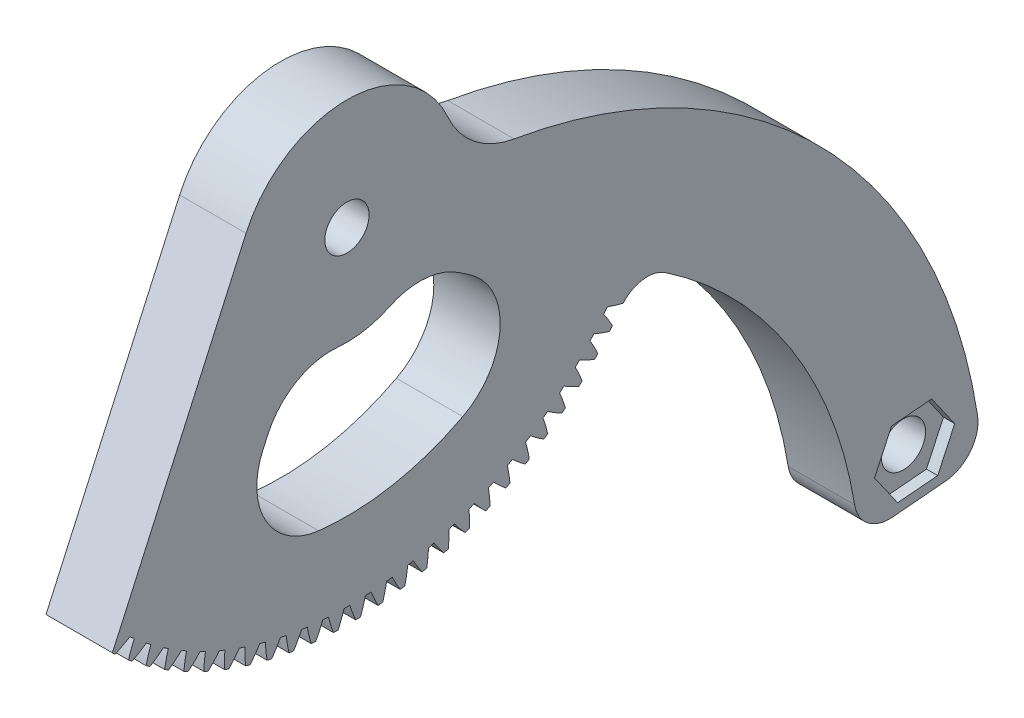
SolidWorks part; units mm, degrees
ref_plane "Plane1" through (0, 0, 0) normal (0, 0, 1) x (1, 0, 0)
ref_plane "Plane2" through (0, 0, 0) normal (0, 1, 0) x (1, 0, 0)
ref_plane "Plane3" through (0, 0, 0) normal (1, 0, 0) x (0, 0, -1)
sketch "HoldingSke" plane through (0, 0, 0) normal (0, 1, 0) x (1, 0, 0)
  line L0 (0, 0) -> (-0.1045, -0.9945)
  line L1 (-15, 0) -> (100, 0) construction
  line L2 (0, 0) -> (-2.1039, 2.3779)
  line L3 (0, 0) -> (-11.863, 4.5341)
  line L4 (0, 0) -> (-0.9027, 8.5887)
  line L5 (0, 0) -> (-46.8476, -17.4728)
  line L6 (0, 0) -> (-10.5278, -7.1032)
  line L7 (-2.1039, 2.3779) -> (8.6586, 51.2059)
  line L8 (-76.2, 54.61) -> (-76.1, 54.61)
  line L9 (-71.009, 38.7566) -> (-53.1078, 45.2721)
  line L10 (-76.2, 71.12) -> (104.1128, 71.12)
  line L11 (0, 0) -> (-12.7, 0)
  line L12 (-76.2, 101.6) -> (-76.162, 101.6)
  line L13 (24.9733, 27.94) -> (52.9518, 28.4284)
  line L14 (24.9733, 27.94) -> (24.9743, 27.94)
  line L15 (24.9733, 27.94) -> (100.4006, 29.5858)
  line L16 (-63.627, -1) -> (-12.827, -1)
  circle A0 centre (0, 0) radius 0.4
  circle A1 centre (0, 0) radius 37.5
  circle A2 centre (0, 0) radius 37.5
  circle A3 centre (0, 0) radius 0.4
  dimension "MHD" = 75
  dimension "Hub_dia" = 75
  dimension "Bore" = 0.8
  dimension "MBD" = 0.8
  dimension "Num_teeth" = 96
  dimension "Pitch" = 1
  dimension "Overall_len" = 50
  dimension "Show_teeth" = 96
  dimension "Thickness" = 12.7
  dimension "OAL" = 50.0001
  dimension "T_dim" = 0.1
  dimension "Ap" = 20
  dimension "H" = 19.05
  dimension "Pitch_radius" = 180.3128
  dimension "Width" = 12.7
  dimension "Backlash" = 0.038
  dimension "Addendum_fac" = 1
  dimension "Dedendum_fac" = 1.25
  dimension "Clearance_fac" = 0.25
  dimension "Dedendum_add" = 0.001
  dimension "Module" = 1
sketch "BasProSke" plane through (0, 0, 0) normal (0, 1, 0) x (1, 0, 0)
  line L0 (-10, 0) -> (60, 0) construction
  line L1 (0, 0) -> (0, 49)
  line L2 (0, 0) -> (12.7, 0)
  line L3 (12.7, 0) -> (12.7, 49)
  line L4 (12.7, 49) -> (0, 49)
  dimension "Thickness" = 12.7
  dimension "Diameter" = 98
revolve "Base-Revolve" add sketch "BasProSke" angle 360 about L0
sketch "TooCutSke" plane through (0, 0, 0) normal (1, 0, 0) x (0, 0, -1)
  line L1 (0, 0) -> (0, 107) construction
  line L2 (0, 0) -> (-0.8519, 47.9924) construction
  line L3 (0, 0) -> (-3.1407, 95.9378) construction
  line L4 (-0.8519, 47.9924) -> (-1.5703, 47.9689) construction
  arc A0 (0.4157, 46.7472) -> (-0.4157, 46.7472) centre (0, 0) ccw
  arc A1 (1.2815, 49.0086) -> (-1.2815, 49.0086) centre (0, 0) ccw
  circle A2 centre (0, 0) radius 48 construction
  circle A3 centre (0, 0) radius 45.1052 construction
  arc A4 (-0.4157, 46.7472) -> (-1.2815, 49.0086) centre (-18.7436, 41.0264) ccw
  arc A5 (1.2815, 49.0086) -> (0.4157, 46.7472) centre (18.7436, 41.0264) ccw
  dimension "Root_dia" = 93.498
  dimension "Overcut_dia" = 98.0508
  dimension "Pitch_dia" = 96
  dimension "Base_dia" = 90.2105
  dimension "Flank_rad" = 19.2
  dimension "Half_ang" = 1.875
  dimension "Half_CT" = 0.7189
extrude "ToothCut" cut sketch "TooCutSke" along normal through all
fillet "Breaks" [suppressed] radius 0.02
fillet "RootFillets" [suppressed] radius 0.251
pattern_circular "TeethCuts" count 96 over 360 about axis through (0, 0, 0) along (1, 0, 0) of "ToothCut", "RootFillets", "Breaks"
sketch "HubNeaOneSke" plane through (0, 0, 0) normal (-1, 0, 0) x (0, 0, 1)
  circle A0 centre (0, 0) radius 37.5
  dimension "Diameter" = 75
extrude "HubNearOne" [suppressed] add sketch "HubNeaOneSke" along normal blind 37.3001
sketch "HubNeaBotSke" plane through (0, 0, 0) normal (-1, 0, 0) x (0, 0, 1)
  circle A0 centre (0, 0) radius 37.5
  dimension "Diameter" = 75
extrude "HubNearBoth" [suppressed] add sketch "HubNeaBotSke" along normal blind 18.65
ref_plane "FarPln" through (12.7, 0, 0) normal (1, 0, 0) x (0, 0, -1)
sketch "HubFarSke" plane through (12.7, 0, 0) normal (1, 0, 0) x (0, 0, -1)
  circle A0 centre (0, 0) radius 37.5
  dimension "Diameter" = 75
extrude "HubFar" [suppressed] add sketch "HubFarSke" along normal blind 18.65
sketch "BorSke" plane through (0, 0, 0) normal (1, 0, 0) x (0, 0, -1)
  circle A0 centre (0, 0) radius 0.4
  dimension "Diameter" = 0.8
extrude "Bore" cut sketch "BorSke" along normal mid plane 100.0001
sketch "KeySke" plane through (0, 0, 0) normal (1, 0, 0) x (0, 0, -1)
  line L0 (-0.05, 0) -> (-0.05, 0.5)
  line L1 (-0.05, 0.5) -> (0.05, 0.5)
  line L2 (0.05, 0.5) -> (0.05, 0)
  line L3 (0, 0) -> (0, 34) construction
  line L4 (-0.05, 0) -> (0.05, 0)
  dimension "Offset" = 0.5
  dimension "Width" = 0.1
extrude "Keyway" [suppressed] cut sketch "KeySke" along normal mid plane 100.0001
pattern_circular "Keyway2" [suppressed] count 2 every 90 about axis through (-10, 0, 0) along (1, 0, 0)
sketch "Croquis2" plane through (12.7, 0, 0) normal (1, 0, 0) x (0, 0, -1)
  line L4 (78.2913, -74.7181) -> (85.9012, -74.0523)
  line L5 (-14.4729, 6.923) -> (-33.6475, -35.6208)
  arc A0 (-33.6475, -35.6208) -> (40.4538, -27.7628) centre (0, 0.4) ccw
  arc A1 (48.3959, -8.954) -> (40.4538, -27.7628) centre (0, 0.4) ccw
  arc A2 (-33.7385, -35.5347) -> (-33.252, -35.9904) centre (0, 0) ccw construction
  arc A66 (85.9012, -74.0523) -> (90.4783, -68.2125) centre (85.4584, -68.9917) ccw
  arc A67 (90.4783, -68.2125) -> (23.9847, -0.5832) centre (10.16, -80.6788) ccw
  arc A68 (14.5249, 6.8066) -> (23.9847, -0.5832) centre (26.1448, 11.9318) ccw
  arc A69 (14.5249, 6.8066) -> (-14.4729, 6.923) centre (0, 0.4) ccw
  arc A96 (45.6754, -28.0395) -> (40.4538, -27.7628) centre (42.8342, -32.2506) ccw
  arc A97 (72.8346, -70.4738) -> (45.6754, -28.0395) centre (10.16, -80.6788) ccw
  arc A98 (72.8346, -70.4738) -> (78.2913, -74.7181) centre (77.8486, -69.6574) ccw
extrude "Cortar-Extruir1" cut sketch "Croquis2" against normal through all contours A69 A68 A67 A1 L5
sketch "Croquis3" plane through (12.7, 0, 0) normal (1, 0, 0) x (0, 0, -1)
  line L0 (78.2913, -74.7181) -> (85.9012, -74.0523) construction
  line L1 (78.2913, -74.7181) -> (85.9012, -74.0523)
  line L2 (23.9847, -0.5832) -> (26.1016, -24.7798)
  line L4 (39.6344, -28.8117) -> (26.1016, -24.7798)
  arc A1 (90.4783, -68.2125) -> (23.9847, -0.5832) centre (10.16, -80.6788) ccw construction
  arc A2 (85.9012, -74.0523) -> (90.4783, -68.2125) centre (85.4584, -68.9917) ccw construction
  arc A3 (72.8346, -70.4738) -> (78.2913, -74.7181) centre (77.8486, -69.6574) ccw construction
  arc A4 (72.8346, -70.4738) -> (45.6754, -28.0395) centre (10.16, -80.6788) ccw construction
  arc A6 (90.4783, -68.2125) -> (23.9847, -0.5832) centre (10.16, -80.6788) ccw
  arc A7 (85.9012, -74.0523) -> (90.4783, -68.2125) centre (85.4584, -68.9917) ccw
  arc A8 (72.8346, -70.4738) -> (78.2913, -74.7181) centre (77.8486, -69.6574) ccw
  arc A9 (72.8346, -70.4738) -> (45.6754, -28.0395) centre (10.16, -80.6788) ccw
  arc A13 (39.6344, -28.8117) -> (45.6754, -28.0395) centre (43.0946, -31.8647) cw
extrude "Saliente-Extruir1" add sketch "Croquis3" against normal through all
sketch "Croquis4" plane through (12.7, 0, 0) normal (1, 0, 0) x (0, 0, -1)
  line L0 (78.2913, -74.7181) -> (85.9012, -74.0523) construction
  circle A0 centre (0, 0.4) radius 3.175
  circle A1 centre (81.4431, -68.0681) radius 3.175
  arc A2 (90.4783, -68.2125) -> (23.9847, -0.5832) centre (10.16, -80.6788) ccw construction
  arc A3 (90.4783, -68.2125) -> (23.9847, -0.5832) centre (10.16, -80.6788) ccw construction
  circle A4 centre (10.16, -80.6788) radius 72.39 construction
  circle A5 centre (10.16, -80.6788) radius 81.715 construction
  arc A6 (14.5249, 6.8066) -> (-14.4729, 6.923) centre (0, 0.4) ccw construction
  point P8 (0, 0)
  dimension "D1" = 6.35
  dimension "D2" = 6.35
  dimension "D3" = 144.78
  dimension "D4" = 163.43
extrude "Cortar-Extruir2" cut sketch "Croquis4" against normal through all
sketch "Croquis5" plane through (12.7, 0, 0) normal (1, 0, 0) x (0, 0, -1)
  line L0 (78.2913, -74.7181) -> (85.9012, -74.0523) construction
  line L1 (83.8831, -62.8355) -> (78.1316, -63.3387)
  line L2 (78.1316, -63.3387) -> (75.6916, -68.5713)
  line L3 (75.6916, -68.5713) -> (79.0031, -73.3007)
  line L4 (79.0031, -73.3007) -> (84.7547, -72.7975)
  line L5 (84.7547, -72.7975) -> (87.1946, -67.5649)
  line L6 (87.1946, -67.5649) -> (83.8831, -62.8355)
  circle A0 centre (81.4431, -68.0681) radius 5 construction
  dimension "D1" = 10
extrude "Cortar-Extruir3" cut sketch "Croquis5" against normal blind 3.2 contours L1 L2 L3 L4 L5 L6
ref_plane "Plano1" through (6.35, 0, 0) normal (1, 0, 0) x (0, 0, -1)
sketch "Croquis7" plane through (12.7, 0, 0) normal (1, 0, 0) x (0, 0, -1)
  line L0 (-12.0435, -21.2056) -> (-11.3475, -19.6613)
  line L1 (17.5581, -14.2325) -> (16.023, -13.2028)
  arc A0 (-1.3117, -13.8126) -> (6.1461, -12.4819) centre (0, 0.4) ccw
  arc A1 (-4.0575, -35.2504) -> (16.619, -31.3997) centre (0, 0.4) ccw
  arc A2 (17.5581, -14.2325) -> (16.619, -31.3997) centre (11.9872, -22.5371) cw
  arc A3 (-12.0435, -21.2056) -> (-4.0575, -35.2504) centre (-2.9267, -25.3145) ccw
  arc A4 (-11.3475, -19.6613) -> (-1.3117, -13.8126) centre (-2.2307, -23.7703) cw
  arc A5 (16.023, -13.2028) -> (6.1461, -12.4819) centre (10.4522, -21.5073) ccw
  dimension "D1" = 10
extrude "Cortar-Extruir4" cut sketch "Croquis7" against normal up to surface (12.7 mm away)
sketch "Croquis8" plane through (12.7, 0, 0) normal (1, 0, 0) x (0, 0, -1)
  line L2 (78.2913, -74.7181) -> (85.9012, -74.0523)
  line L3 (-14.4729, 6.923) -> (-33.6475, -35.6208)
  line L4 (78.2913, -74.7181) -> (85.9012, -74.0523)
  line L5 (-14.4729, 6.923) -> (-33.6475, -35.6208)
  arc A111 (36.834, -28.7876) -> (37.3401, -28.1281) centre (0, 0) ccw
  arc A112 (37.3401, -28.1281) -> (39.6344, -28.8117) centre (43.9588, -10.105) ccw
  arc A113 (45.6754, -28.0395) -> (39.6344, -28.8117) centre (43.0946, -31.8647) ccw
  arc A114 (72.8346, -70.4738) -> (45.6754, -28.0395) centre (10.16, -80.6788) ccw
  arc A115 (72.8346, -70.4738) -> (78.2913, -74.7181) centre (77.8486, -69.6574) ccw
  arc A116 (85.9012, -74.0523) -> (90.4783, -68.2125) centre (85.4584, -68.9917) ccw
  arc A117 (90.4783, -68.2125) -> (23.9847, -0.5832) centre (10.16, -80.6788) ccw
  arc A118 (14.5249, 6.8066) -> (23.9847, -0.5832) centre (26.1448, 11.9318) ccw
  arc A119 (14.5249, 6.8066) -> (-14.4729, 6.923) centre (0, 0.4) ccw
  arc A120 (-33.6475, -35.6208) -> (-33.252, -35.9904) centre (0, 0) ccw
  arc A121 (-33.252, -35.9904) -> (-31.1351, -34.8723) centre (-41.1427, -18.4867) ccw
  arc A122 (-31.1351, -34.8723) -> (-30.51, -35.4204) centre (0, 0) ccw
  arc A123 (-30.51, -35.4204) -> (-31.3422, -37.6652) centre (-12.9584, -43.2037) ccw
  arc A124 (-31.3422, -37.6652) -> (-30.8269, -38.0881) centre (0, 0) ccw
  arc A125 (-30.8269, -38.0881) -> (-28.7876, -36.834) centre (-39.8455, -21.138) ccw
  arc A126 (-28.7876, -36.834) -> (-28.1281, -37.3401) centre (0, 0) ccw
  arc A127 (-28.1281, -37.3401) -> (-28.8117, -39.6344) centre (-10.105, -43.9588) ccw
  arc A128 (-28.8117, -39.6344) -> (-28.2698, -40.0227) centre (0, 0) ccw
  arc A129 (-28.2698, -40.0227) -> (-26.3169, -38.6379) centre (-38.3777, -23.6988) ccw
  arc A130 (-26.3169, -38.6379) -> (-25.6257, -39.0998) centre (0, 0) ccw
  arc A131 (-25.6257, -39.0998) -> (-26.1578, -41.4339) centre (-7.2083, -44.5255) ccw
  arc A132 (-26.1578, -41.4339) -> (-25.5917, -41.7859) centre (0, 0) ccw
  arc A133 (-25.5917, -41.7859) -> (-23.7336, -40.2764) centre (-36.7456, -26.1581) ccw
  arc A134 (-23.7336, -40.2764) -> (-23.0136, -40.6921) centre (0, 0) ccw
  arc A135 (-23.0136, -40.6921) -> (-23.3918, -43.056) centre (-4.2808, -44.9017) ccw
  arc A136 (-23.3918, -43.056) -> (-22.804, -43.3703) centre (0, 0) ccw
  arc A137 (-22.804, -43.3703) -> (-21.0485, -41.7424) centre (-34.9561, -28.5053) ccw
  arc A138 (-21.0485, -41.7424) -> (-20.3029, -42.1101) centre (0, 0) ccw
  arc A139 (-20.3029, -42.1101) -> (-20.5258, -44.4937) centre (-1.3349, -45.0855) ccw
  arc A140 (-20.5258, -44.4937) -> (-19.9186, -44.7688) centre (0, 0) ccw
  arc A141 (-19.9186, -44.7688) -> (-18.2734, -43.0297) centre (-33.0169, -30.7305) ccw
  arc A142 (-18.2734, -43.0297) -> (-17.5053, -43.3478) centre (0, 0) ccw
  arc A143 (-17.5053, -43.3478) -> (-17.5718, -45.7409) centre (1.6167, -45.0763) ccw
  arc A144 (-17.5718, -45.7409) -> (-16.9479, -45.9757) centre (0, 0) ccw
  arc A145 (-16.9479, -45.9757) -> (-15.42, -44.1327) centre (-30.9363, -32.8242) ccw
  arc A146 (-15.42, -44.1327) -> (-14.6328, -44.3999) centre (0, 0) ccw
  arc A147 (-14.6328, -44.3999) -> (-14.5426, -46.7922) centre (4.5614, -44.874) ccw
  arc A148 (-14.5426, -46.7922) -> (-13.9047, -46.9857) centre (0, 0) ccw
  arc A149 (-13.9047, -46.9857) -> (-12.5006, -45.0467) centre (-28.7233, -34.7772) ccw
  arc A150 (-12.5006, -45.0467) -> (-11.6976, -45.2619) centre (0, 0) ccw
  arc A151 (-11.6976, -45.2619) -> (-11.4511, -47.6432) centre (7.4865, -44.4796) ccw
  arc A152 (-11.4511, -47.6432) -> (-10.8019, -47.7946) centre (0, 0) ccw
  arc A153 (-10.8019, -47.7946) -> (-9.5276, -45.7678) centre (-26.3873, -36.5813) ccw
  arc A154 (-9.5276, -45.7678) -> (-8.7122, -45.93) centre (0, 0) ccw
  arc A155 (-8.7122, -45.93) -> (-8.3105, -48.2901) centre (10.3796, -43.8947) ccw
  arc A156 (-8.3105, -48.2901) -> (-7.6528, -48.3987) centre (0, 0) ccw
  arc A157 (-7.6528, -48.3987) -> (-6.5138, -46.293) centre (-23.9382, -38.2288) ccw
  arc A158 (-6.5138, -46.293) -> (-5.6896, -46.4015) centre (0, 0) ccw
  arc A159 (-5.6896, -46.4015) -> (-5.1344, -48.7303) centre (13.2282, -43.1219) ccw
  arc A160 (-5.1344, -48.7303) -> (-4.471, -48.7956) centre (0, 0) ccw
  arc A161 (-4.471, -48.7956) -> (-3.4722, -46.6199) centre (-21.3867, -39.7126) ccw
  arc A162 (-3.4722, -46.6199) -> (-2.6426, -46.6742) centre (0, 0) ccw
  arc A163 (-2.6426, -46.6742) -> (-1.9363, -48.9617) centre (16.0202, -42.1644) ccw
  arc A164 (-1.9363, -48.9617) -> (-1.2701, -48.9835) centre (0, 0) ccw
  arc A165 (-1.2701, -48.9835) -> (-0.4157, -46.7472) centre (-18.7436, -41.0264) ccw
  arc A166 (-0.4157, -46.7472) -> (0.4157, -46.7472) centre (0, 0) ccw
  arc A167 (0.4157, -46.7472) -> (1.2701, -48.9835) centre (18.7436, -41.0264) ccw
  arc A168 (1.2701, -48.9835) -> (1.9363, -48.9617) centre (0, 0) ccw
  arc A169 (1.9363, -48.9617) -> (2.6426, -46.6742) centre (-16.0202, -42.1644) ccw
  arc A170 (2.6426, -46.6742) -> (3.4722, -46.6199) centre (0, 0) ccw
  arc A171 (3.4722, -46.6199) -> (4.471, -48.7956) centre (21.3867, -39.7126) ccw
  arc A172 (4.471, -48.7956) -> (5.1344, -48.7303) centre (0, 0) ccw
  arc A173 (5.1344, -48.7303) -> (5.6896, -46.4015) centre (-13.2282, -43.1219) ccw
  arc A174 (5.6896, -46.4015) -> (6.5138, -46.293) centre (0, 0) ccw
  arc A175 (6.5138, -46.293) -> (7.6528, -48.3987) centre (23.9382, -38.2288) ccw
  arc A176 (7.6528, -48.3987) -> (8.3105, -48.2901) centre (0, 0) ccw
  arc A177 (8.3105, -48.2901) -> (8.7122, -45.93) centre (-10.3796, -43.8947) ccw
  arc A178 (8.7122, -45.93) -> (9.5276, -45.7678) centre (0, 0) ccw
  arc A179 (9.5276, -45.7678) -> (10.8019, -47.7946) centre (26.3873, -36.5813) ccw
  arc A180 (10.8019, -47.7946) -> (11.4511, -47.6432) centre (0, 0) ccw
  arc A181 (11.4511, -47.6432) -> (11.6976, -45.2619) centre (-7.4865, -44.4796) ccw
  arc A182 (11.6976, -45.2619) -> (12.5006, -45.0467) centre (0, 0) ccw
  arc A183 (12.5006, -45.0467) -> (13.9047, -46.9857) centre (28.7233, -34.7772) ccw
  arc A184 (13.9047, -46.9857) -> (14.5426, -46.7922) centre (0, 0) ccw
  arc A185 (14.5426, -46.7922) -> (14.6328, -44.3999) centre (-4.5614, -44.874) ccw
  arc A186 (14.6328, -44.3999) -> (15.42, -44.1327) centre (0, 0) ccw
  arc A187 (15.42, -44.1327) -> (16.9479, -45.9757) centre (30.9363, -32.8242) ccw
  arc A188 (16.9479, -45.9757) -> (17.5718, -45.7409) centre (0, 0) ccw
  arc A189 (17.5718, -45.7409) -> (17.5053, -43.3478) centre (-1.6167, -45.0763) ccw
  arc A190 (17.5053, -43.3478) -> (18.2734, -43.0297) centre (0, 0) ccw
  arc A191 (18.2734, -43.0297) -> (19.9186, -44.7688) centre (33.0169, -30.7305) ccw
  arc A192 (19.9186, -44.7688) -> (20.5258, -44.4937) centre (0, 0) ccw
  arc A193 (20.5258, -44.4937) -> (20.3029, -42.1101) centre (1.3349, -45.0855) ccw
  arc A194 (20.3029, -42.1101) -> (21.0485, -41.7424) centre (0, 0) ccw
  arc A195 (21.0485, -41.7424) -> (22.804, -43.3703) centre (34.9561, -28.5053) ccw
  arc A196 (22.804, -43.3703) -> (23.3918, -43.056) centre (0, 0) ccw
  arc A197 (23.3918, -43.056) -> (23.0136, -40.6921) centre (4.2808, -44.9017) ccw
  arc A198 (23.0136, -40.6921) -> (23.7336, -40.2764) centre (0, 0) ccw
  arc A199 (23.7336, -40.2764) -> (25.5917, -41.7859) centre (36.7456, -26.1581) ccw
  arc A200 (25.5917, -41.7859) -> (26.1578, -41.4339) centre (0, 0) ccw
  arc A201 (26.1578, -41.4339) -> (25.6257, -39.0998) centre (7.2083, -44.5255) ccw
  arc A202 (25.6257, -39.0998) -> (26.3169, -38.6379) centre (0, 0) ccw
  arc A203 (26.3169, -38.6379) -> (28.2698, -40.0227) centre (38.3777, -23.6988) ccw
  arc A204 (28.2698, -40.0227) -> (28.8117, -39.6344) centre (0, 0) ccw
  arc A205 (28.8117, -39.6344) -> (28.1281, -37.3401) centre (10.105, -43.9588) ccw
  arc A206 (28.1281, -37.3401) -> (28.7876, -36.834) centre (0, 0) ccw
  arc A207 (28.7876, -36.834) -> (30.8269, -38.0881) centre (39.8455, -21.138) ccw
  arc A208 (30.8269, -38.0881) -> (31.3422, -37.6652) centre (0, 0) ccw
  arc A209 (31.3422, -37.6652) -> (30.51, -35.4204) centre (12.9584, -43.2037) ccw
  arc A210 (30.51, -35.4204) -> (31.1351, -34.8723) centre (0, 0) ccw
  arc A211 (31.1351, -34.8723) -> (33.252, -35.9904) centre (41.1427, -18.4867) ccw
  arc A212 (33.252, -35.9904) -> (33.7385, -35.5347) centre (0, 0) ccw
  arc A213 (33.7385, -35.5347) -> (32.7613, -33.3491) centre (15.7563, -42.2637) ccw
  arc A214 (32.7613, -33.3491) -> (33.3491, -32.7613) centre (0, 0) ccw
  arc A215 (33.3491, -32.7613) -> (35.5347, -33.7385) centre (42.2637, -15.7563) ccw
  arc A216 (35.5347, -33.7385) -> (35.9904, -33.252) centre (0, 0) ccw
  arc A217 (35.9904, -33.252) -> (34.8723, -31.1351) centre (18.4867, -41.1427) ccw
  arc A218 (34.8723, -31.1351) -> (35.4204, -30.51) centre (0, 0) ccw
  arc A219 (35.4204, -30.51) -> (37.6652, -31.3422) centre (43.2037, -12.9584) ccw
  arc A220 (37.6652, -31.3422) -> (38.0881, -30.8269) centre (0, 0) ccw
  arc A221 (38.0881, -30.8269) -> (36.834, -28.7876) centre (21.138, -39.8455) ccw
  arc A222 (36.834, -28.7876) -> (37.3401, -28.1281) centre (0, 0) ccw
  arc A223 (37.3401, -28.1281) -> (39.6344, -28.8117) centre (43.9588, -10.105) ccw
  arc A224 (45.6754, -28.0395) -> (39.6344, -28.8117) centre (43.0946, -31.8647) ccw
  arc A225 (72.8346, -70.4738) -> (45.6754, -28.0395) centre (10.16, -80.6788) ccw
  arc A226 (72.8346, -70.4738) -> (78.2913, -74.7181) centre (77.8486, -69.6574) ccw
  arc A227 (85.9012, -74.0523) -> (90.4783, -68.2125) centre (85.4584, -68.9917) ccw
  arc A228 (90.4783, -68.2125) -> (23.9847, -0.5832) centre (10.16, -80.6788) ccw
  arc A229 (14.5249, 6.8066) -> (23.9847, -0.5832) centre (26.1448, 11.9318) ccw
  arc A230 (14.5249, 6.8066) -> (-14.4729, 6.923) centre (0, 0.4) ccw
  arc A231 (-33.6475, -35.6208) -> (-33.252, -35.9904) centre (0, 0) ccw
  arc A232 (-33.252, -35.9904) -> (-31.1351, -34.8723) centre (-41.1427, -18.4867) ccw
  arc A233 (-31.1351, -34.8723) -> (-30.51, -35.4204) centre (0, 0) ccw
  arc A234 (-30.51, -35.4204) -> (-31.3422, -37.6652) centre (-12.9584, -43.2037) ccw
  arc A235 (-31.3422, -37.6652) -> (-30.8269, -38.0881) centre (0, 0) ccw
  arc A236 (-30.8269, -38.0881) -> (-28.7876, -36.834) centre (-39.8455, -21.138) ccw
  arc A237 (-28.7876, -36.834) -> (-28.1281, -37.3401) centre (0, 0) ccw
  arc A238 (-28.1281, -37.3401) -> (-28.8117, -39.6344) centre (-10.105, -43.9588) ccw
  arc A239 (-28.8117, -39.6344) -> (-28.2698, -40.0227) centre (0, 0) ccw
  arc A240 (-28.2698, -40.0227) -> (-26.3169, -38.6379) centre (-38.3777, -23.6988) ccw
  arc A241 (-26.3169, -38.6379) -> (-25.6257, -39.0998) centre (0, 0) ccw
  arc A242 (-25.6257, -39.0998) -> (-26.1578, -41.4339) centre (-7.2083, -44.5255) ccw
  arc A243 (-26.1578, -41.4339) -> (-25.5917, -41.7859) centre (0, 0) ccw
  arc A244 (-25.5917, -41.7859) -> (-23.7336, -40.2764) centre (-36.7456, -26.1581) ccw
  arc A245 (-23.7336, -40.2764) -> (-23.0136, -40.6921) centre (0, 0) ccw
  arc A246 (-23.0136, -40.6921) -> (-23.3918, -43.056) centre (-4.2808, -44.9017) ccw
  arc A247 (-23.3918, -43.056) -> (-22.804, -43.3703) centre (0, 0) ccw
  arc A248 (-22.804, -43.3703) -> (-21.0485, -41.7424) centre (-34.9561, -28.5053) ccw
  arc A249 (-21.0485, -41.7424) -> (-20.3029, -42.1101) centre (0, 0) ccw
  arc A250 (-20.3029, -42.1101) -> (-20.5258, -44.4937) centre (-1.3349, -45.0855) ccw
  arc A251 (-20.5258, -44.4937) -> (-19.9186, -44.7688) centre (0, 0) ccw
  arc A252 (-19.9186, -44.7688) -> (-18.2734, -43.0297) centre (-33.0169, -30.7305) ccw
  arc A253 (-18.2734, -43.0297) -> (-17.5053, -43.3478) centre (0, 0) ccw
  arc A254 (-17.5053, -43.3478) -> (-17.5718, -45.7409) centre (1.6167, -45.0763) ccw
  arc A255 (-17.5718, -45.7409) -> (-16.9479, -45.9757) centre (0, 0) ccw
  arc A256 (-16.9479, -45.9757) -> (-15.42, -44.1327) centre (-30.9363, -32.8242) ccw
  arc A257 (-15.42, -44.1327) -> (-14.6328, -44.3999) centre (0, 0) ccw
  arc A258 (-14.6328, -44.3999) -> (-14.5426, -46.7922) centre (4.5614, -44.874) ccw
  arc A259 (-14.5426, -46.7922) -> (-13.9047, -46.9857) centre (0, 0) ccw
  arc A260 (-13.9047, -46.9857) -> (-12.5006, -45.0467) centre (-28.7233, -34.7772) ccw
  arc A261 (-12.5006, -45.0467) -> (-11.6976, -45.2619) centre (0, 0) ccw
  arc A262 (-11.6976, -45.2619) -> (-11.4511, -47.6432) centre (7.4865, -44.4796) ccw
  arc A263 (-11.4511, -47.6432) -> (-10.8019, -47.7946) centre (0, 0) ccw
  arc A264 (-10.8019, -47.7946) -> (-9.5276, -45.7678) centre (-26.3873, -36.5813) ccw
  arc A265 (-9.5276, -45.7678) -> (-8.7122, -45.93) centre (0, 0) ccw
  arc A266 (-8.7122, -45.93) -> (-8.3105, -48.2901) centre (10.3796, -43.8947) ccw
  arc A267 (-8.3105, -48.2901) -> (-7.6528, -48.3987) centre (0, 0) ccw
  arc A268 (-7.6528, -48.3987) -> (-6.5138, -46.293) centre (-23.9382, -38.2288) ccw
  arc A269 (-6.5138, -46.293) -> (-5.6896, -46.4015) centre (0, 0) ccw
  arc A270 (-5.6896, -46.4015) -> (-5.1344, -48.7303) centre (13.2282, -43.1219) ccw
  arc A271 (-5.1344, -48.7303) -> (-4.471, -48.7956) centre (0, 0) ccw
  arc A272 (-4.471, -48.7956) -> (-3.4722, -46.6199) centre (-21.3867, -39.7126) ccw
  arc A273 (-3.4722, -46.6199) -> (-2.6426, -46.6742) centre (0, 0) ccw
  arc A274 (-2.6426, -46.6742) -> (-1.9363, -48.9617) centre (16.0202, -42.1644) ccw
  arc A275 (-1.9363, -48.9617) -> (-1.2701, -48.9835) centre (0, 0) ccw
  arc A276 (-1.2701, -48.9835) -> (-0.4157, -46.7472) centre (-18.7436, -41.0264) ccw
  arc A277 (-0.4157, -46.7472) -> (0.4157, -46.7472) centre (0, 0) ccw
  arc A278 (0.4157, -46.7472) -> (1.2701, -48.9835) centre (18.7436, -41.0264) ccw
  arc A279 (1.2701, -48.9835) -> (1.9363, -48.9617) centre (0, 0) ccw
  arc A280 (1.9363, -48.9617) -> (2.6426, -46.6742) centre (-16.0202, -42.1644) ccw
  arc A281 (2.6426, -46.6742) -> (3.4722, -46.6199) centre (0, 0) ccw
  arc A282 (3.4722, -46.6199) -> (4.471, -48.7956) centre (21.3867, -39.7126) ccw
  arc A283 (4.471, -48.7956) -> (5.1344, -48.7303) centre (0, 0) ccw
  arc A284 (5.1344, -48.7303) -> (5.6896, -46.4015) centre (-13.2282, -43.1219) ccw
  arc A285 (5.6896, -46.4015) -> (6.5138, -46.293) centre (0, 0) ccw
  arc A286 (6.5138, -46.293) -> (7.6528, -48.3987) centre (23.9382, -38.2288) ccw
  arc A287 (7.6528, -48.3987) -> (8.3105, -48.2901) centre (0, 0) ccw
  arc A288 (8.3105, -48.2901) -> (8.7122, -45.93) centre (-10.3796, -43.8947) ccw
  arc A289 (8.7122, -45.93) -> (9.5276, -45.7678) centre (0, 0) ccw
  arc A290 (9.5276, -45.7678) -> (10.8019, -47.7946) centre (26.3873, -36.5813) ccw
  arc A291 (10.8019, -47.7946) -> (11.4511, -47.6432) centre (0, 0) ccw
  arc A292 (11.4511, -47.6432) -> (11.6976, -45.2619) centre (-7.4865, -44.4796) ccw
  arc A293 (11.6976, -45.2619) -> (12.5006, -45.0467) centre (0, 0) ccw
  arc A294 (12.5006, -45.0467) -> (13.9047, -46.9857) centre (28.7233, -34.7772) ccw
  arc A295 (13.9047, -46.9857) -> (14.5426, -46.7922) centre (0, 0) ccw
  arc A296 (14.5426, -46.7922) -> (14.6328, -44.3999) centre (-4.5614, -44.874) ccw
  arc A297 (14.6328, -44.3999) -> (15.42, -44.1327) centre (0, 0) ccw
  arc A298 (15.42, -44.1327) -> (16.9479, -45.9757) centre (30.9363, -32.8242) ccw
  arc A299 (16.9479, -45.9757) -> (17.5718, -45.7409) centre (0, 0) ccw
  arc A300 (17.5718, -45.7409) -> (17.5053, -43.3478) centre (-1.6167, -45.0763) ccw
  arc A301 (17.5053, -43.3478) -> (18.2734, -43.0297) centre (0, 0) ccw
  arc A302 (18.2734, -43.0297) -> (19.9186, -44.7688) centre (33.0169, -30.7305) ccw
  arc A303 (19.9186, -44.7688) -> (20.5258, -44.4937) centre (0, 0) ccw
  arc A304 (20.5258, -44.4937) -> (20.3029, -42.1101) centre (1.3349, -45.0855) ccw
  arc A305 (20.3029, -42.1101) -> (21.0485, -41.7424) centre (0, 0) ccw
  arc A306 (21.0485, -41.7424) -> (22.804, -43.3703) centre (34.9561, -28.5053) ccw
  arc A307 (22.804, -43.3703) -> (23.3918, -43.056) centre (0, 0) ccw
  arc A308 (23.3918, -43.056) -> (23.0136, -40.6921) centre (4.2808, -44.9017) ccw
  arc A309 (23.0136, -40.6921) -> (23.7336, -40.2764) centre (0, 0) ccw
  arc A310 (23.7336, -40.2764) -> (25.5917, -41.7859) centre (36.7456, -26.1581) ccw
  arc A311 (25.5917, -41.7859) -> (26.1578, -41.4339) centre (0, 0) ccw
  arc A312 (26.1578, -41.4339) -> (25.6257, -39.0998) centre (7.2083, -44.5255) ccw
  arc A313 (25.6257, -39.0998) -> (26.3169, -38.6379) centre (0, 0) ccw
  arc A314 (26.3169, -38.6379) -> (28.2698, -40.0227) centre (38.3777, -23.6988) ccw
  arc A315 (28.2698, -40.0227) -> (28.8117, -39.6344) centre (0, 0) ccw
  arc A316 (28.8117, -39.6344) -> (28.1281, -37.3401) centre (10.105, -43.9588) ccw
  arc A317 (28.1281, -37.3401) -> (28.7876, -36.834) centre (0, 0) ccw
  arc A318 (28.7876, -36.834) -> (30.8269, -38.0881) centre (39.8455, -21.138) ccw
  arc A319 (30.8269, -38.0881) -> (31.3422, -37.6652) centre (0, 0) ccw
  arc A320 (31.3422, -37.6652) -> (30.51, -35.4204) centre (12.9584, -43.2037) ccw
  arc A321 (30.51, -35.4204) -> (31.1351, -34.8723) centre (0, 0) ccw
  arc A322 (31.1351, -34.8723) -> (33.252, -35.9904) centre (41.1427, -18.4867) ccw
  arc A323 (33.252, -35.9904) -> (33.7385, -35.5347) centre (0, 0) ccw
  arc A324 (33.7385, -35.5347) -> (32.7613, -33.3491) centre (15.7563, -42.2637) ccw
  arc A325 (32.7613, -33.3491) -> (33.3491, -32.7613) centre (0, 0) ccw
  arc A326 (33.3491, -32.7613) -> (35.5347, -33.7385) centre (42.2637, -15.7563) ccw
  arc A327 (35.5347, -33.7385) -> (35.9904, -33.252) centre (0, 0) ccw
  arc A328 (35.9904, -33.252) -> (34.8723, -31.1351) centre (18.4867, -41.1427) ccw
  arc A329 (34.8723, -31.1351) -> (35.4204, -30.51) centre (0, 0) ccw
  arc A330 (35.4204, -30.51) -> (37.6652, -31.3422) centre (43.2037, -12.9584) ccw
  arc A331 (37.6652, -31.3422) -> (38.0881, -30.8269) centre (0, 0) ccw
  arc A332 (38.0881, -30.8269) -> (36.834, -28.7876) centre (21.138, -39.8455) ccw
  dimension "D1" = 0
extrude "Cortar-Extruir5" cut sketch "Croquis8" against normal blind 1.5875
mirror "Simetría1" about plane through (6.35, 0, 0) normal (1, 0, 0) of "Cortar-Extruir5"
sketch "Croquis11" plane through (6.35, 0, 0) normal (1, 0, 0) x (0, 0, -1)
  circle A4 centre (0, 0) radius 48
  arc A6 (22.804, -43.3703) -> (23.3918, -43.056) centre (0, 0) ccw construction
  arc A7 (22.804, -43.3703) -> (23.3918, -43.056) centre (0, 0) ccw
  circle A9 centre (0, 0) radius 49 construction
  dimension "D1" = 96
equation "' \"Module@HoldingSke\" = 6.35"
equation "' \"Num_teeth@HoldingSke\" = 12"
equation "' \"Ap@HoldingSke\" =  20"
equation "' \"Ap@HoldingSke\" = 20"
equation "' \"Width@HoldingSke\" = 0.5 * 25.4"
equation "' \"Hub_dia@HoldingSke\"= 1 * 25.4"
equation "' \"Hub_dia@HoldingSke\" = 1 * 25.4"
equation "' \"Overall_len@HoldingSke\" = 1.0 * 25.4"
equation "' \"Bore@HoldingSke\" = 0.75 * 25.4"
equation "' \"T_dim@HoldingSke\" = 0.1 * 25.4"
equation "' \"Width@KeySke\" = 0.25 * 25.4"
equation "' \"Show_teeth@HoldingSke\" = 13"
equation "' \"Backlash@HoldingSke\" = 0.009 * 25.4"
equation "' \"Addendum_fac@HoldingSke\" = 1.0"
equation "' \"Dedendum_fac@HoldingSke\" = 1.25"
equation "' \"Dedendum_add@HoldingSke\" = 0.00005 * 25.4"
equation "' \"Clearance_fac@HoldingSke\" = 0.25"
equation "\"Pitch@HoldingSke\" = 1 / \"Module@HoldingSke\""
equation "\"Overcut_dia@TooCutSke\" = (\"Num_teeth@HoldingSke\" + 2 * \"Addendum_fac@HoldingSke\") / \"Pitch@HoldingSke\" + 0.002 * 25.4"
equation "\"Pitch_dia@TooCutSke\" = \"Num_teeth@HoldingSke\" / \"Pitch@HoldingSke\""
equation "\"Base_dia@TooCutSke\" = \"Num_teeth@HoldingSke\" / \"Pitch@HoldingSke\" * cos((\"Ap@HoldingSke\"  * 3.14159265 / 180))"
equation "\"Root_dia@TooCutSke\" = (\"Num_teeth@HoldingSke\" + 2) / \"Pitch@HoldingSke\" - 2 * (\"Addendum_fac@HoldingSke\" + \"Dedendum_fac@HoldingSke\") / \"Pitch@HoldingSke\" - \"Dedendum_add@HoldingSke\" * 2"
equation "\"Half_ang@TooCutSke\" = 180 / \"Num_teeth@HoldingSke\""
equation "\"Half_CT@TooCutSke\" = \"Num_teeth@HoldingSke\" / \"Pitch@HoldingSke\" * sin((3.14159265 / 2 / \"Num_teeth@HoldingSke\")) / 2 - 7 * \"Backlash@HoldingSke\" / 4"
equation "\"Flank_rad@TooCutSke\" = \"Num_teeth@HoldingSke\" / \"Pitch@HoldingSke\" / 5"
equation "\"Radius@RootFillets\" = \"Clearance_fac@HoldingSke\" / \"Pitch@HoldingSke\" + \"Dedendum_add@HoldingSke\""
equation "\"Break_rad@Breaks\" = 0.02 / \"Pitch@HoldingSke\""
equation "\"Thickness@HoldingSke\" = \"Width@HoldingSke\""
equation "\"OAL@HoldingSke\" = \"Thickness@HoldingSke\""
equation "\"MHD@HoldingSke\" = (\"Num_teeth@HoldingSke\" + 2) / \"Pitch@HoldingSke\" - 2 * (\"Addendum_fac@HoldingSke\" + \"Dedendum_fac@HoldingSke\")  / \"Pitch@HoldingSke\" - \"Dedendum_add@HoldingSke\" * 2"
equation "\"MBD@HoldingSke\" = (\"Num_teeth@HoldingSke\" + 2) / \"Pitch@HoldingSke\" - 2 * (\"Addendum_fac@HoldingSke\" + \"Dedendum_fac@HoldingSke\")  / \"Pitch@HoldingSke\" - \"Dedendum_add@HoldingSke\" * 2 - 0.002 * 25.4"
equation "\"MHD@HoldingSke\" = ((sgn( \"MHD@HoldingSke\" - \"Hub_dia@HoldingSke\" )-1)*( \"MHD@HoldingSke\" - \"Hub_dia@HoldingSke\" ))/-2+ \"Hub_dia@HoldingSke\""
equation "\"MBD@HoldingSke\" = ((sgn( \"MBD@HoldingSke\" - \"Bore@HoldingSke\" )-1)*( \"MBD@HoldingSke\" - \"Bore@HoldingSke\" ))/-2+ \"Bore@HoldingSke\""
equation "\"OAL@HoldingSke\" = ((sgn( \"OAL@HoldingSke\" - \"Overall_len@HoldingSke\" )+1)*( \"OAL@HoldingSke\" - \"Overall_len@HoldingSke\" ))/2 + \"Overall_len@HoldingSke\" + 0.000002 * 25.4"
equation "\"Num_teeth@TeethCuts\" = int( \"Show_teeth@HoldingSke\" ) + 1"
equation "\"Num_teeth@TeethCuts\" = ((sgn( \"Num_teeth@TeethCuts\" - \"Num_teeth@HoldingSke\" )-1)*( \"Num_teeth@TeethCuts\" - \"Num_teeth@HoldingSke\" ))/-2+ \"Num_teeth@HoldingSke\""
equation "\"Num_teeth@TeethCuts\" = ((sgn( \"Num_teeth@TeethCuts\" - 2.0)+1)*( \"Num_teeth@TeethCuts\" - 2.0))/2 +2.0"
equation "\"Angle@TeethCuts\" = 360.0 / \"Num_teeth@HoldingSke\""
equation "\"Diameter@BasProSke\" = (\"Num_teeth@HoldingSke\" + 2 * \"Addendum_fac@HoldingSke\") / \"Pitch@HoldingSke\""
equation "\"Thickness@BasProSke\"  = \"Thickness@HoldingSke\""
equation "' \"Fillet_rad@BasProSke\" =  \"Thickness@HoldingSke\" * 0.05"
equation "' \"Fillet_rad@BasProSke\" = \"Thickness@HoldingSke\" * 0.05"
equation "\"MHD@HoldingSke\" = ((sgn( \"MHD@HoldingSke\" - \"Root_dia@TooCutSke\" )-1)*( \"MHD@HoldingSke\" - \"Root_dia@TooCutSke\" ))/-2+ \"Root_dia@TooCutSke\""
equation "\"Diameter@HubNeaOneSke\" = \"MHD@HoldingSke\""
equation "\"Length@HubNearOne\" = \"OAL@HoldingSke\" - \"Thickness@BasProSke\""
equation "\"Diameter@HubNeaBotSke\" = \"MHD@HoldingSke\""
equation "\"Length@HubNearBoth\" = ( \"OAL@HoldingSke\" - \"Thickness@BasProSke\" ) / 2.0"
equation "\"Thickness@FarPln\" = \"Thickness@BasProSke\""
equation "\"Diameter@HubFarSke\" = \"MHD@HoldingSke\""
equation "\"Length@HubFar\" = ( \"OAL@HoldingSke\" - \"Thickness@BasProSke\" ) / 2.0"
equation "\"Diameter@BorSke\" = \"MBD@HoldingSke\""
equation "\"D1@Bore\" = \"OAL@HoldingSke\" * 2.0"
equation "\"D1@Keyway\" = \"OAL@HoldingSke\" * 2.0"
equation "\"Offset@KeySke\" = \"T_dim@HoldingSke\" + \"MBD@HoldingSke\" / 2.0"
